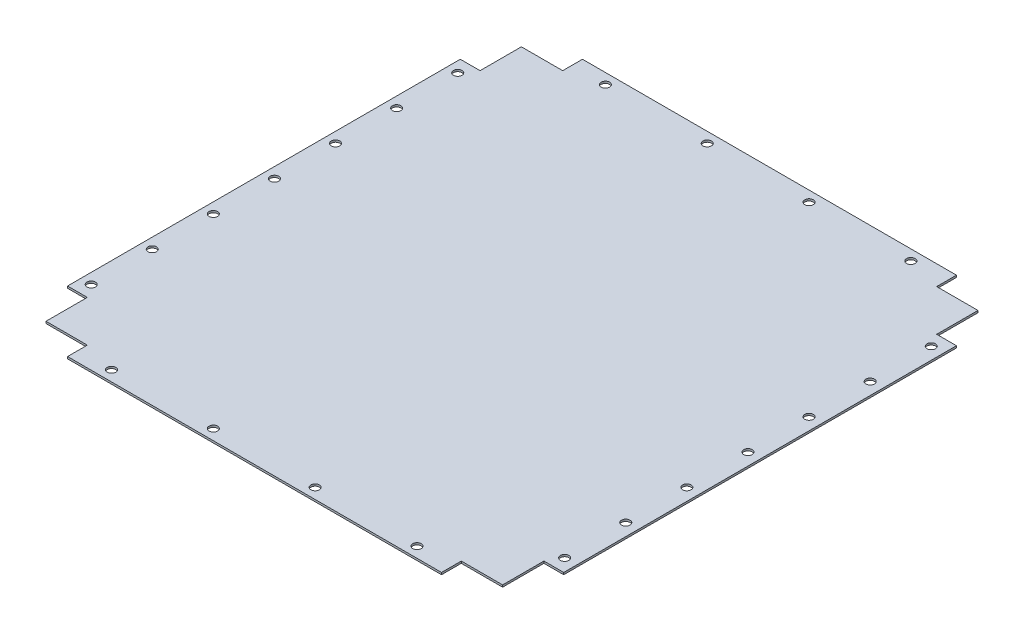
SolidWorks part; units mm, degrees
material "6061 Alloy"
ref_plane "Front Plane" through (0, 0, 0) normal (0, 0, 1) x (1, 0, 0)
ref_plane "Top Plane" through (0, 0, 0) normal (0, 1, 0) x (1, 0, 0)
ref_plane "Right Plane" through (0, 0, 0) normal (1, 0, 0) x (0, 0, -1)
sketch "Sketch1" plane through (0, 0, 0) normal (0, 1, 0) x (1, 0, 0)
  line L1 (-309.405, 321.105) -> (309.405, 321.105)
  line L2 (-309.405, 321.105) -> (-309.405, -321.105)
  line L3 (-309.405, -321.105) -> (309.405, -321.105)
  line L4 (309.405, 321.105) -> (309.405, -321.105)
  line L5 (-309.405, 321.105) -> (309.405, -321.105) construction
  line L6 (-309.405, -321.105) -> (309.405, 321.105) construction
  point P0 (0, 0)
  dimension "D1" = 618.81
  dimension "D2" = 642.21
extrude "Boss-Extrude1" add sketch "Sketch1" along normal blind 2.5
sketch "Sketch2" plane through (0, 2.5, 0) normal (0, 1, 0) x (1, 0, 0)
  line L0 (0, 321.105) -> (0, -321.105) construction
  line L1 (309.405, 321.105) -> (-309.405, 321.105) construction
  line L2 (-309.405, -321.105) -> (309.405, -321.105) construction
  line L3 (-309.405, 0) -> (309.405, 0) construction
  line L4 (-309.405, 321.105) -> (-309.405, -321.105) construction
  line L5 (309.405, -321.105) -> (309.405, 321.105) construction
  line L6 (-309.405, 321.105) -> (-233.205, 321.105)
  line L7 (-233.205, 321.105) -> (-233.205, 296.445)
  line L8 (-233.205, 296.445) -> (-284.745, 296.445)
  line L9 (-284.745, 296.445) -> (-284.745, 244.905)
  line L10 (-284.745, 244.905) -> (-309.405, 244.905)
  line L11 (-309.405, 244.905) -> (-309.405, 321.105)
  line L12 (-284.745, -244.905) -> (-309.405, -244.905)
  line L13 (-284.745, -296.445) -> (-284.745, -244.905)
  line L14 (-233.205, -296.445) -> (-284.745, -296.445)
  line L15 (-233.205, -321.105) -> (-233.205, -296.445)
  line L16 (-309.405, -321.105) -> (-233.205, -321.105)
  line L17 (-309.405, -244.905) -> (-309.405, -321.105)
  line L18 (284.745, -296.445) -> (284.745, -244.905)
  line L19 (233.205, -296.445) -> (284.745, -296.445)
  line L20 (233.205, -321.105) -> (233.205, -296.445)
  line L21 (309.405, -321.105) -> (233.205, -321.105)
  line L22 (309.405, -244.905) -> (309.405, -321.105)
  line L23 (284.745, -244.905) -> (309.405, -244.905)
  line L24 (284.745, 244.905) -> (309.405, 244.905)
  line L25 (284.745, 296.445) -> (284.745, 244.905)
  line L26 (233.205, 296.445) -> (284.745, 296.445)
  line L27 (233.205, 321.105) -> (233.205, 296.445)
  line L28 (309.405, 321.105) -> (233.205, 321.105)
  line L29 (309.405, 244.905) -> (309.405, 321.105)
  dimension "D1" = 51.54
  dimension "D2" = 76.2
extrude "Cut-Extrude1" cut sketch "Sketch2" against normal blind 2.5
sketch "Sketch3" plane through (0, 0, 0) normal (0, -1, 0) x (-1, 0, 0)
  line L0 (0.9982, 292.0982) -> (0.9982, -292.1018) construction
  line L1 (-278.4018, 292.0982) -> (280.3982, 292.0982) construction
  line L2 (280.3982, -292.1018) -> (-278.4018, -292.1018) construction
  circle A0 centre (-294.2768, -228.6018) radius 5.334
  circle A1 centre (-294.2768, -152.4018) radius 5.334
  circle A2 centre (-294.2768, -76.2018) radius 5.334
  circle A3 centre (-294.2768, -0.0018) radius 5.334
  circle A4 centre (-294.2768, 76.1982) radius 5.334
  circle A5 centre (-294.2768, 152.3982) radius 5.334
  circle A6 centre (-294.2768, 228.5982) radius 5.334
  circle A7 centre (296.2732, -228.6018) radius 5.334
  circle A8 centre (296.2732, -152.4018) radius 5.334
  circle A9 centre (296.2732, -76.2018) radius 5.334
  circle A10 centre (296.2732, -0.0018) radius 5.334
  circle A11 centre (296.2732, 76.1982) radius 5.334
  circle A12 centre (296.2732, 152.3982) radius 5.334
  circle A13 centre (296.2732, 228.5982) radius 5.334
  dimension "D1" = 7
extrude "Cut-Extrude2" cut sketch "Sketch3" against normal blind 10
sketch "Sketch4" plane through (0, 0, 0) normal (0, -1, 0) x (1, 0, 0)
  line L0 (0, 0) -> (-266.4361, 0) construction
  circle A0 centre (189.5018, 307.9768) radius 5.334
  circle A1 centre (62.5018, 307.9768) radius 5.334
  circle A2 centre (-64.4982, 307.9768) radius 5.334
  circle A3 centre (-191.4982, 307.9768) radius 5.334
  circle A4 centre (-191.4982, -307.9768) radius 5.334
  circle A5 centre (-64.4982, -307.9768) radius 5.334
  circle A6 centre (62.5018, -307.9768) radius 5.334
  circle A7 centre (189.5018, -307.9768) radius 5.334
  dimension "D1" = 4
extrude "Cut-Extrude3" cut sketch "Sketch4" against normal blind 10
